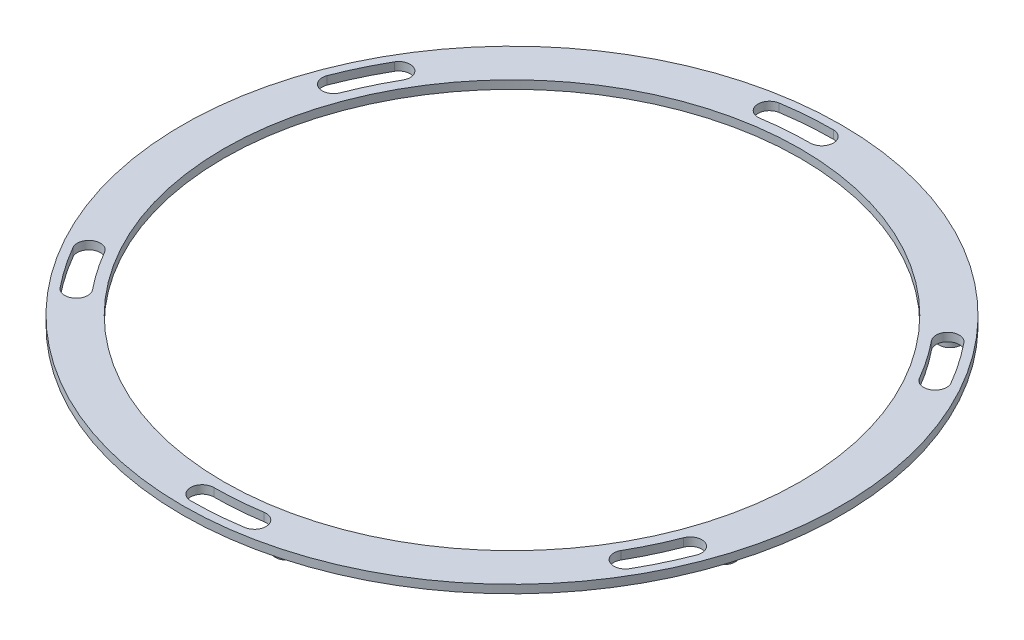
SolidWorks part; units mm, degrees
ref_plane "Front Plane" through (0, 0, 0) normal (0, 0, 1) x (1, 0, 0)
ref_plane "Top Plane" through (0, 0, 0) normal (0, 1, 0) x (1, 0, 0)
ref_plane "Right Plane" through (0, 0, 0) normal (1, 0, 0) x (0, 0, -1)
sketch "Sketch1" plane through (0, 0, 0) normal (0, 1, 0) x (1, 0, 0)
  circle A0 centre (0, 0) radius 200
  circle A1 centre (0, 0) radius 175
  dimension "D1" = 400
  dimension "D2" = 350
extrude "Boss-Extrude1" add sketch "Sketch1" along normal blind 5
sketch "Sketch2" plane through (0, 5, 0) normal (0, 1, 0) x (1, 0, 0)
  line L0 (-29.4097, 185.6854) -> (0, 0) construction
  line L1 (0, 0) -> (0, 188) construction
  line L2 (0, 0) -> (-45.4813, 182.4156) construction
  arc A0 (0, 188) -> (-29.4097, 185.6854) centre (0, 0) ccw construction
  arc A1 (0, 195) -> (-30.5047, 192.5992) centre (0, 0) ccw
  arc A2 (0, 181) -> (-28.3146, 178.7716) centre (0, 0) ccw
  arc A3 (0, 181) -> (0, 195) centre (0, 188) ccw
  arc A4 (-30.5047, 192.5992) -> (-28.3146, 178.7716) centre (-29.4097, 185.6854) ccw
  circle A5 centre (-45.4813, 182.4156) radius 2
  point P4 (-14.7503, 187.4205)
  dimension "D2" = 188
  dimension "D3" = 7
  dimension "D4" = 4
  dimension "D1" = 9
  dimension "D5" = 5
extrude "Cut-Extrude1" cut sketch "Sketch2" against normal blind 21
pattern_circular "CirPattern1" count 6 over 360 about axis through (0, 0, 0) along (0, 1, 0) of "Cut-Extrude1"
scale "Scale1" scale about centroid uniform scaling yes scale factor 0.225
sketch "Sketch3" plane through (0, 3.0625, 0) normal (0, 1, 0) x (1, 0, 0)
  circle A12 centre (-10.2333, 41.0435) radius 1.5
  circle A13 centre (30.4281, 29.384) radius 1.5
  circle A14 centre (40.6614, -11.6595) radius 1.5
  circle A15 centre (10.2333, -41.0435) radius 1.5
  circle A16 centre (-30.4281, -29.384) radius 1.5
  circle A17 centre (-40.6614, 11.6595) radius 1.5
  dimension "D1" = 3
  dimension "D2" = 6
extrude "Boss-Extrude2" add sketch "Sketch3" against normal blind 2.26
sketch "Sketch4" plane through (0, 1.9375, 0) normal (0, -1, 0) x (1, 0, 0)
  circle A0 centre (0, 0) radius 41.965 construction
  arc A1 (6.8636, 43.3348) -> (0, 43.875) centre (0, 0) ccw construction
  arc A2 (-31.6493, 25.6291) -> (-35.2689, 20.3625) centre (0, 0) ccw construction
  arc A4 (-34.0973, 27.6114) -> (-37.9969, 21.9375) centre (0, 0) ccw construction
  circle A5 centre (0, 0) radius 38.175
  circle A8 centre (0, 0) radius 39.375 construction
  dimension "D1" = 1.24
  dimension "D2" = 1.91
  dimension "D3" = 1.2
